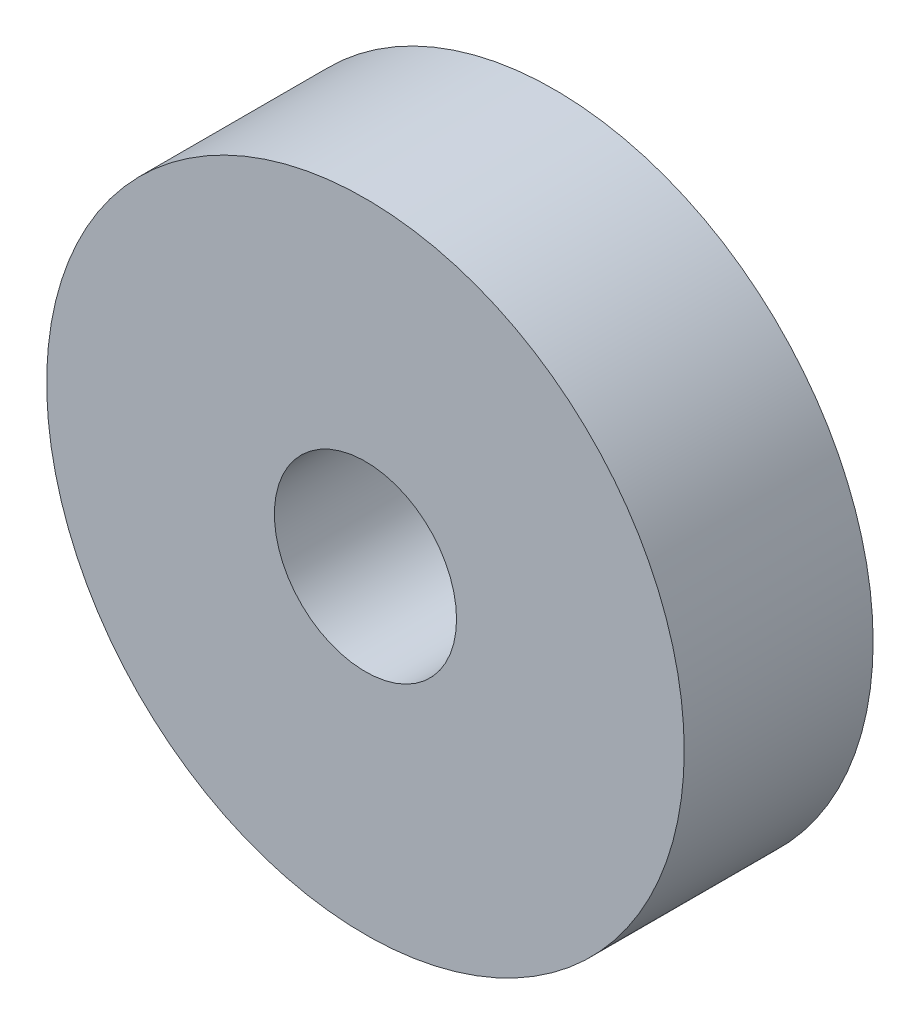
SolidWorks part; units mm, degrees
ref_plane "Přední rovina" through (0, 0, 0) normal (0, 0, 1) x (1, 0, 0)
ref_plane "Vrchní rovina" through (0, 0, 0) normal (0, 1, 0) x (1, 0, 0)
ref_plane "Pravá rovina" through (0, 0, 0) normal (1, 0, 0) x (0, 0, -1)
sketch "Skica1" plane through (0, 0, 0) normal (0, 0, 1) x (1, 0, 0)
  circle A0 centre (0, 0) radius 33.75
  circle A1 centre (0, 0) radius 9.6429
  dimension "dm" = 19.2857
  dimension "Df" = 67.5
extrude "Přidat vysunutím1" add sketch "Skica1" along normal blind 20
sketch "Skica2" plane through (0, 0, 20) normal (0, 0, 1) x (1, 0, 0)
  circle A0 centre (0, 0) radius 33.75 construction
  circle A1 centre (0, 0) radius 33.75
  circle A2 centre (0, 0) radius 37.5
  circle A3 centre (0, 0) radius 40.5
  point P5 (-98.768, 42.0738)
  dimension "D1" = 75
  dimension "D2" = 81
equation "\"m\"= 3mm'Modul"
equation "\"z\"= 25mm'Počet zubů"
equation "\"d\"= \"m\" * \"z\"'Průměr roztečné kružnice"
equation "\"df\"= \"d\" - \"m\" * 2.5'Průměr patní kružnice"
equation "\"da\"= \"d\" + \"m\" * 2'Průměr hlavové kružnice"
equation "\"Df@Skica1\"= \"df\""
equation "\"dm@Skica1\"= \"df\" / 3.5"
equation "\"D1@Skica2\"= \"d\""
equation "\"D2@Skica2\"= \"da\""
